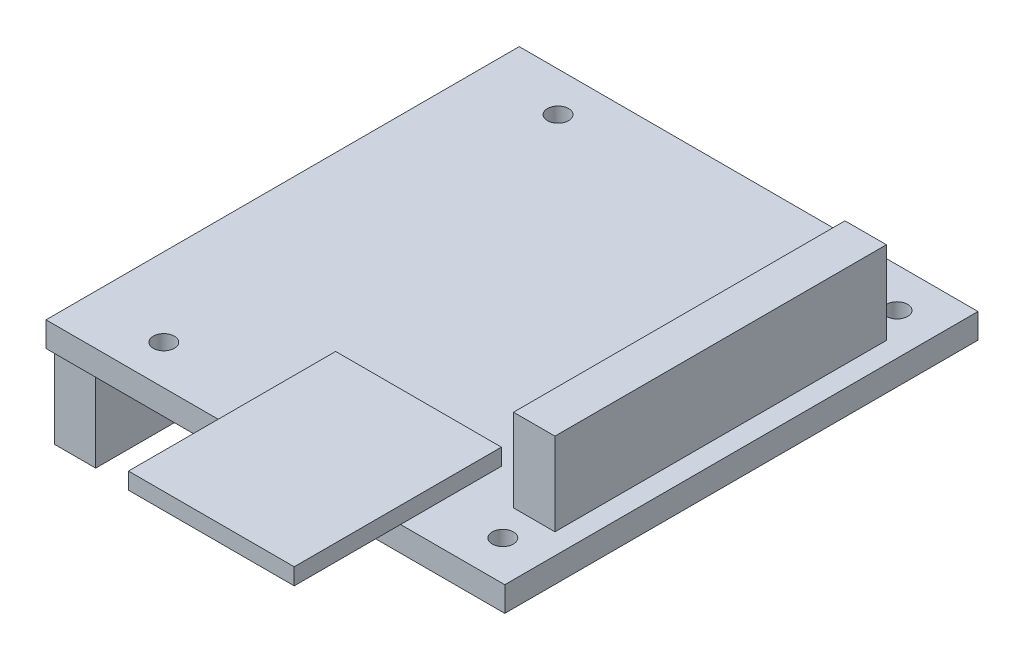
SolidWorks part; units mm, degrees
ref_plane "Face" through (0, 0, 0) normal (0, 0, 1) x (1, 0, 0)
ref_plane "Dessus" through (0, 0, 0) normal (0, 1, 0) x (1, 0, 0)
ref_plane "Droite" through (0, 0, 0) normal (1, 0, 0) x (0, 0, -1)
sketch "Esquisse1" plane through (0, 0, 0) normal (0, 1, 0) x (1, 0, 0)
  line L0 (0, 52.335) -> (55.36, 52.335) construction
  line L1 (0, 0) -> (55.36, 0)
  line L2 (0, 0) -> (0, 57.1)
  line L3 (0, 57.1) -> (55.36, 57.1)
  line L4 (55.36, 0) -> (55.36, 57.1)
  line L5 (9.45, 57.1) -> (9.45, 0) construction
  line L6 (50.36, 57.1) -> (50.36, 0) construction
  line L7 (0, 4.765) -> (55.36, 4.765) construction
  line L8 (55.36, 28.55) -> (0, 28.55) construction
  line L9 (27.68, 52.335) -> (27.68, 4.765) construction
  circle A0 centre (9.45, 52.335) radius 1.275
  circle A1 centre (50.36, 52.335) radius 1.275
  circle A2 centre (9.45, 4.765) radius 1.275
  circle A3 centre (50.36, 4.765) radius 1.275
  point P25 (27.68, 28.55)
  dimension "D3" = 2.55
  dimension "D1" = 55.36
  dimension "D2" = 57.1
  dimension "D4" = 47.57
  dimension "D5" = 40.91
  dimension "D6" = 5
extrude "Extrusion1" add sketch "Esquisse1" along normal blind 3
sketch "Esquisse2" plane through (0, 3, 0) normal (0, 1, 0) x (1, 0, 0)
  line L0 (50.36, 52.335) -> (50.36, 4.765) construction
  line L1 (47.86, 48.55) -> (52.86, 48.55)
  line L2 (47.86, 48.55) -> (47.86, 8.55)
  line L3 (52.86, 48.55) -> (52.86, 8.55)
  line L4 (47.86, 8.55) -> (52.86, 8.55)
  line L5 (55.36, 28.55) -> (0, 28.55) construction
  line L7 (55.36, 0) -> (55.36, 57.1) construction
  line L8 (0, 57.1) -> (0, 0) construction
  dimension "D1" = 5
  dimension "D2" = 40
extrude "Extrusion2" add sketch "Esquisse2" along normal blind 10
sketch "Esquisse3" plane through (0, 3, 0) normal (0, 1, 0) x (1, 0, 0)
  line L1 (42.7803, 12.1696) -> (22.7803, 12.1696)
  line L2 (42.7803, 12.1696) -> (42.7803, -12.8304)
  line L3 (42.7803, -12.8304) -> (22.7803, -12.8304)
  line L4 (22.7803, 12.1696) -> (22.7803, -12.8304)
  dimension "D1" = 20
  dimension "D2" = 25
extrude "Extrusion3" add sketch "Esquisse3" along normal blind 2
sketch "Esquisse4" plane through (0, 0, 0) normal (0, -1, 0) x (1, 0, 0)
  line L1 (0.5, -56.6) -> (5.5, -56.6)
  line L2 (0.5, -56.6) -> (0.5, -0.5)
  line L3 (0.5, -0.5) -> (5.5, -0.5)
  line L4 (5.5, -56.6) -> (5.5, -0.5)
  line L5 (0, 0) -> (55.36, 0) construction
  line L6 (55.36, -57.1) -> (0, -57.1) construction
  line L7 (0, -57.1) -> (0, 0) construction
  dimension "D1" = 5
  dimension "D2" = 0.5
  dimension "D3" = 0.5
  dimension "D4" = 0.5
extrude "Extrusion4" add sketch "Esquisse4" along normal blind 10
sketch "Esquisse5" plane through (0, 0, 0) normal (0, -1, 0) x (1, 0, 0)
  line L1 (22.2442, -54.933) -> (12.2442, -54.933)
  line L2 (22.2442, -54.933) -> (22.2442, -59.933)
  line L3 (22.2442, -59.933) -> (12.2442, -59.933)
  line L4 (12.2442, -54.933) -> (12.2442, -59.933)
  dimension "D1" = 10
  dimension "D2" = 5
extrude "Extrusion5" add sketch "Esquisse5" along normal blind 5
